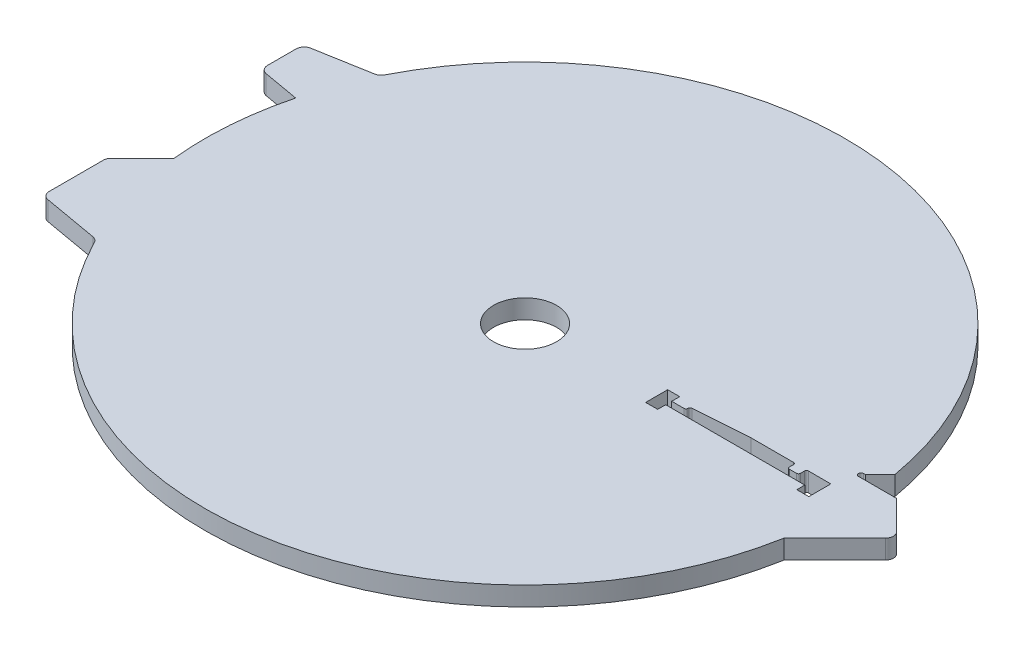
SolidWorks part; units mm, degrees
ref_plane "Front Plane" through (0, 0, 0) normal (0, 0, 1) x (1, 0, 0)
ref_plane "Top Plane" through (0, 0, 0) normal (0, 1, 0) x (1, 0, 0)
ref_plane "Right Plane" through (0, 0, 0) normal (1, 0, 0) x (0, 0, -1)
sketch "Sketch1" plane through (0, 0, 0) normal (0, 1, 0) x (1, 0, 0)
  circle A0 centre (0, 0) radius 80
  circle A1 centre (0, 0) radius 7.875
  dimension "D1" = 160
  dimension "D2" = 15.75
extrude "Boss-Extrude1" add sketch "Sketch1" along normal blind 4.7625
sketch "Sketch2" plane through (0, 4.7625, 0) normal (0, 1, 0) x (1, 0, 0)
  line L0 (34.45, 0) -> (70.55, 0) construction
  line L1 (70.55, 0) -> (70.55, 3) construction
  line L2 (70.55, 3) -> (52.95, 3) construction
  line L3 (52.95, 3) -> (52.95, 2) construction
  line L4 (52.95, 2) -> (39.45, 2) construction
  line L5 (39.45, 2) -> (39.45, 1) construction
  line L6 (39.45, 1) -> (34.45, 1) construction
  line L7 (34.45, 1) -> (34.45, 0) construction
  line L8 (34.2, 0) -> (70.8, 0)
  line L9 (70.8, 0) -> (70.8, 3)
  line L10 (70.3, 3.5) -> (67.3, 3.5)
  line L11 (52.95, 3.5) -> (39.165, 2.5326)
  line L12 (34.2, 1) -> (34.2, 0)
  line L13 (63.55, 3.5) -> (52.95, 3.5)
  line L14 (34.7, 1.5) -> (38.2, 1.5)
  line L15 (64.05, 3) -> (64.05, 2)
  line L16 (64.55, 1.5) -> (66.3, 1.5)
  line L17 (66.8, 3) -> (66.8, 2)
  line L18 (38.7, 2) -> (38.7, 2.0339)
  line L19 (52.5, 0) -> (52.5, -15.0605) construction
  line L20 (39.165, 2.5326) -> (38.7, 2.5) construction
  line L21 (38.7, 2.0339) -> (38.7, 2.5) construction
  circle A0 centre (0, 0) radius 52.5 construction
  arc A1 (66.3, 1.5) -> (66.8, 2) centre (66.3, 2) ccw
  arc A2 (64.05, 2) -> (64.55, 1.5) centre (64.55, 2) ccw
  arc A3 (38.2, 1.5) -> (38.7, 2) centre (38.2, 2) ccw
  arc A4 (63.55, 3.5) -> (64.05, 3) centre (63.55, 3) cw
  arc A5 (67.3, 3.5) -> (66.8, 3) centre (67.3, 3) ccw
  arc A6 (70.8, 3) -> (70.3, 3.5) centre (70.3, 3) ccw
  arc A7 (34.7, 1.5) -> (34.2, 1) centre (34.7, 1) ccw
  arc A8 (38.7, 2.0339) -> (39.165, 2.5326) centre (39.2, 2.0339) cw
  point P4 (52.5, 0)
  dimension "D1" = 105
  dimension "D15" = 0.5
  dimension "D16" = 0.5
  dimension "D2" = 36.1
  dimension "D3" = 1
  dimension "D4" = 5
  dimension "D5" = 2
  dimension "D6" = 18.5
  dimension "D7" = 3
  dimension "D8" = 0.25
  dimension "D9" = 0.25
  dimension "D10" = 0.5
  dimension "D11" = 3.75
  dimension "D12" = 1.5
  dimension "D13" = 6.5
  dimension "D14" = 4.25
  dimension "D17" = 90
  dimension "D18" = 1
extrude "Cut-Extrude1" cut sketch "Sketch2" against normal through all
sketch "Sketch4" plane through (0, 4.7625, 0) normal (0, 1, 0) x (1, 0, 0)
  line L0 (0, 0) -> (-88, 0) construction
  line L1 (-88, 32.5) -> (-60, 37.4372)
  line L2 (-88, 32.5) -> (-88, 16.5)
  line L3 (-88, -32.5) -> (-60, -37.4372)
  line L4 (-60, 37.4372) -> (-60, -37.4372)
  line L5 (-88, -16.5) -> (-71.5, 0)
  line L6 (78.7518, 14.0766) -> (91.4142, 1.4142)
  line L7 (91.4142, -1.4142) -> (78.7518, -14.0766)
  line L8 (78.7518, -14.0766) -> (78.7518, 14.0766)
  line L9 (-71.5, 0) -> (-88, 16.5)
  line L10 (-88, -16.5) -> (-88, -32.5)
  circle A2 centre (0, 0) radius 80 construction
  arc A4 (91.4142, 1.4142) -> (91.4142, -1.4142) centre (90, 0) cw
  dimension "D1" = 2
  dimension "D4" = 80
  dimension "D2" = 65
  dimension "D3" = 88
  dimension "D5" = 60
  dimension "D6" = 90
  dimension "D7" = 45
  dimension "D8" = 71.5
  dimension "D9" = 90
extrude "Boss-Extrude2" add sketch "Sketch4" against normal up to surface (4.7625 mm away) up to face at (55.059, 0, -2.1453)
sketch "Sketch3" plane through (0, 4.7625, 0) normal (0, 1, 0) x (1, 0, 0)
  line L0 (0, 0) -> (74.7708, 0) construction
  line L1 (0, 0) -> (74.9372, 9.2011) construction
  line L2 (75.1872, 9.8261) -> (74.6872, 9.8261)
  line L3 (74.6872, 8.5761) -> (84.2523, 8.5761)
  line L4 (78.7518, 14.0766) -> (84.2523, 8.5761)
  line L5 (91.4142, 1.4142) -> (78.7518, 14.0766) construction
  line L7 (78.8539, 13.4928) -> (75.1872, 9.8261)
  circle A0 centre (74.9372, 9.2011) radius 0.625 construction
  arc A1 (74.6872, 9.8261) -> (74.6872, 8.5761) centre (74.6872, 9.2011) ccw
  arc A3 (78.7518, 14.0766) -> (78.8539, 13.4928) centre (0, 0) cw
  arc A4 (78.7518, 14.0766) -> (-71.7594, 35.3637) centre (0, 0) ccw construction
  dimension "D3" = 1.25
  dimension "D1" = 7
  dimension "D2" = 75.5
  dimension "D4" = 0.25
  dimension "D5" = 0.25
  dimension "D6" = 45
extrude "Cut-Extrude2" cut sketch "Sketch3" against normal through all
sketch "Sketch5" plane through (0, 4.7625, 0) normal (0, 1, 0) x (1, 0, 0)
  line L0 (52.5, 0) -> (52.5, -11) construction
  line L1 (43.5, 5) -> (46.5, 5)
  line L2 (43.5, 5) -> (43.5, -11)
  line L3 (43.5, -11) -> (46.5, -11)
  line L4 (46.5, 5) -> (46.5, -11)
  line L5 (58.5, 5) -> (61.5, 5)
  line L6 (58.5, 5) -> (58.5, -11)
  line L7 (58.5, -11) -> (61.5, -11)
  line L8 (61.5, 5) -> (61.5, -11)
  line L9 (34.2, 0) -> (70.8, 0) construction
  line L10 (46.5, -11) -> (52.5, -11) construction
  line L11 (52.5, -11) -> (58.5, -11) construction
  dimension "D1" = 3
  dimension "D2" = 18
  dimension "D3" = 11
  dimension "D4" = 5
extrude "Cut-Extrude3" [suppressed] cut sketch "Sketch5" against normal through all
sketch "Sketch6" plane through (0, 4.7625, 0) normal (0, 1, 0) x (1, 0, 0)
  line L0 (0, 0) -> (107.3946, 0) construction
  line L1 (32.125, 3.5) -> (72.875, 3.5)
  line L2 (32.125, 3.5) -> (32.125, -2)
  line L3 (32.125, -2) -> (72.875, -2)
  line L4 (72.875, 3.5) -> (72.875, -2)
  line L5 (52.5, 0) -> (52.5, -2) construction
  dimension "D1" = 2
  dimension "D2" = 40.75
  dimension "D3" = 5.5
extrude "Cut-Extrude4" [suppressed] cut sketch "Sketch6" against normal through all
sketch "Sketch7" plane through (0, 4.7625, 0) normal (0, 1, 0) x (1, 0, 0)
  line L0 (-88, 22) -> (-77.4246, 20.1353)
  line L1 (-88, 32.5) -> (-88, 16.5) construction
  line L2 (-88, 22) -> (-73.6189, 22) construction
  line L3 (-88, 22) -> (-88, 16.5)
  line L4 (-88, 16.5) -> (-79.5899, 8.0899)
  arc A0 (-77.4246, 20.1353) -> (-79.5899, 8.0899) centre (0, 0) ccw
  arc A1 (-79.5899, 8.0899) -> (-79.5899, -8.0899) centre (0, 0) ccw construction
  dimension "D1" = 10
  dimension "D2" = 22
extrude "Cut-Extrude5" cut sketch "Sketch7" against normal through all
fillet "Fillet1" radius 2 6 edges at (-71.7594, 2.3813, 35.3637) (-88, 2.3813, -32.5) (-71.7594, 2.3813, -35.3637) (-88, 2.3813, 16.5) (-88, 2.3813, -22) (-88, 2.3813, 32.5)
sketch "Sketch8" plane through (0, 4.7625, 0) normal (0, 1, 0) x (1, 0, 0)
  line L0 (34.2, 0) -> (70.8, 0) construction
  line L1 (32.125, -2) -> (35.125, -2)
  line L2 (32.125, -2) -> (32.125, 3.5)
  line L3 (32.125, 3.5) -> (35.125, 3.5)
  line L4 (35.125, -2) -> (35.125, 3.5)
  line L5 (72.875, -2) -> (69.875, -2)
  line L6 (72.875, -2) -> (72.875, 3.5)
  line L7 (72.875, 3.5) -> (69.875, 3.5)
  line L8 (69.875, -2) -> (69.875, 3.5)
  line L9 (52.5, 0) -> (35.125, -2) construction
  line L10 (52.5, 0) -> (69.875, -2) construction
  dimension "D1" = 3
  dimension "D2" = 5.5
  dimension "D3" = 2
  dimension "D4" = 40.75
extrude "Cut-Extrude6" cut sketch "Sketch8" against normal through all
